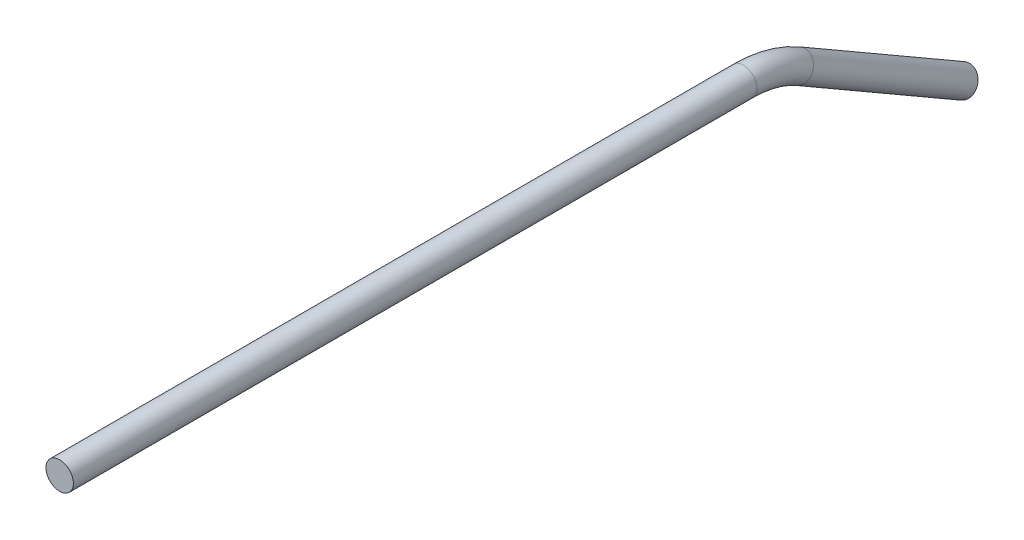
SolidWorks part; units mm, degrees
ref_plane "Front Plane" through (0, 0, 0) normal (0, 0, 1) x (1, 0, 0)
ref_plane "Top Plane" through (0, 0, 0) normal (0, 1, 0) x (1, 0, 0)
ref_plane "Right Plane" through (0, 0, 0) normal (1, 0, 0) x (0, 0, -1)
sketch "Sketch2" plane through (0, 0, 0) normal (0, 0, 1) x (1, 0, 0)
  circle A0 centre (0, 0) radius 3.175
  dimension "D1" = 6.35
sketch "Sketch4" plane through (0, 0, 0) normal (1, 0, 0) x (0, 0, -1)
  line L0 (0, 0) -> (158.2941, 0)
  line L1 (170.9941, -3.403) -> (209.0941, -25.4)
  arc A0 (170.9941, -3.403) -> (158.2941, 0) centre (158.2941, -25.4) ccw
  point P6 (165.1, 0)
  dimension "D4" = 25.4
  dimension "D1" = 165.1
  dimension "D2" = 50.8
  dimension "D3" = 30
sweep "Sweep1" add profiles "Sketch2" path "Sketch4"
